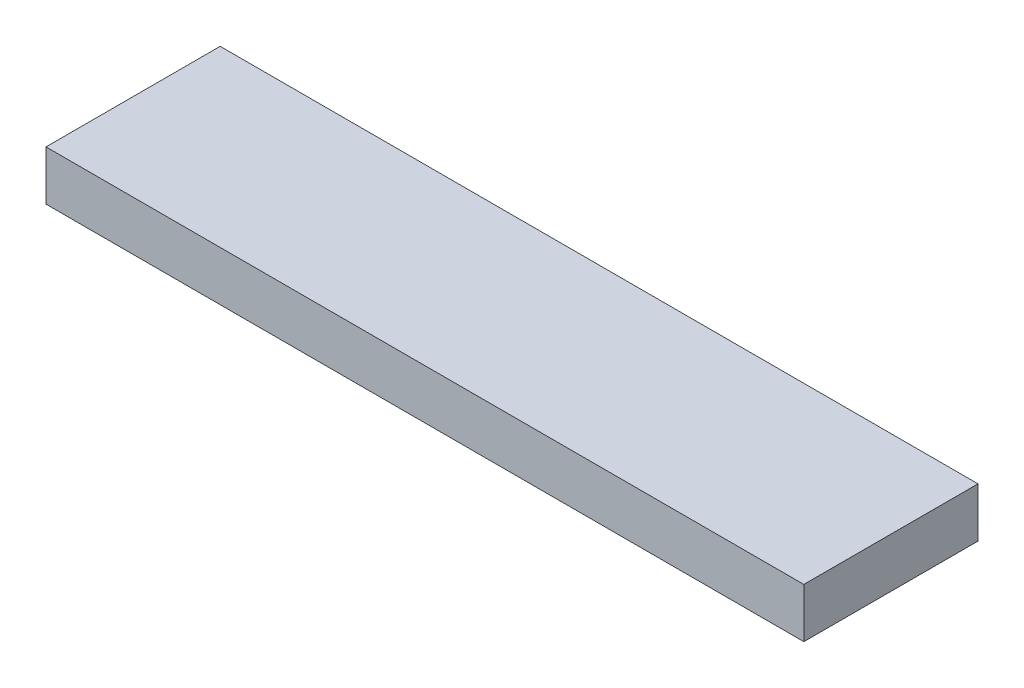
SolidWorks part; units mm, degrees
material "POLYURETHANE (11671)"
ref_plane "Front Plane" through (0, 0, 0) normal (0, 0, 1) x (1, 0, 0)
ref_plane "Top Plane" through (0, 0, 0) normal (0, 1, 0) x (1, 0, 0)
ref_plane "Right Plane" through (0, 0, 0) normal (1, 0, 0) x (0, 0, -1)
sketch "Sketch1" plane through (0, -31.1817, 0) normal (0, 1, 0) x (1, 0, 0)
  line L1 (86.0227, -73.7404) -> (183.0507, -73.7404)
  line L2 (86.0227, -73.7404) -> (86.0227, -51.4392)
  line L3 (86.0227, -51.4392) -> (183.0507, -51.4392)
  line L4 (183.0507, -73.7404) -> (183.0507, -51.4392)
extrude "Boss-Extrude1" add sketch "Sketch1" along normal blind 6.35
